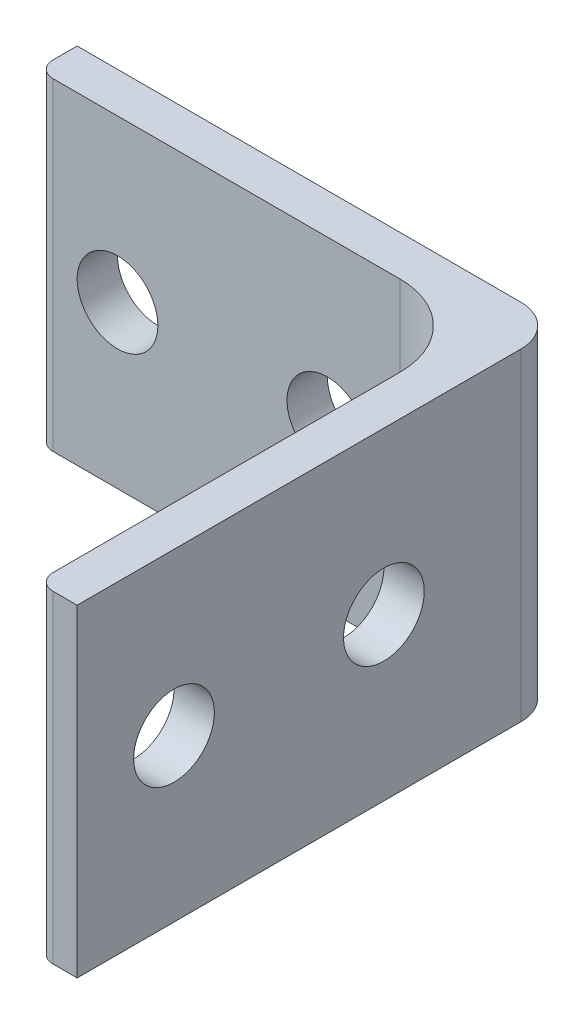
SolidWorks part; units mm, degrees
ref_plane "Front Plane" through (0, 0, 0) normal (0, 0, 1) x (1, 0, 0)
ref_plane "Top Plane" through (0, 0, 0) normal (0, 1, 0) x (1, 0, 0)
ref_plane "Right Plane" through (0, 0, 0) normal (1, 0, 0) x (0, 0, -1)
sketch "Sketch1" plane through (0, 0, 0) normal (0, 1, 0) x (1, 0, 0)
  line L0 (0, 0) -> (34.925, 0)
  line L1 (38.1, -3.175) -> (38.1, -38.1)
  line L2 (38.1, -38.1) -> (36.195, -38.1)
  line L3 (34.925, -36.83) -> (34.925, -9.525)
  line L4 (28.575, -3.175) -> (1.27, -3.175)
  line L5 (0, -1.905) -> (0, 0)
  arc A0 (34.925, -9.525) -> (28.575, -3.175) centre (28.575, -9.525) ccw
  arc A1 (34.925, 0) -> (38.1, -3.175) centre (34.925, -3.175) cw
  arc A2 (36.195, -38.1) -> (34.925, -36.83) centre (36.195, -36.83) cw
  arc A3 (1.27, -3.175) -> (0, -1.905) centre (1.27, -1.905) cw
  point P11 (38.1, 0)
  point P14 (34.925, -38.1)
  point P17 (0, -3.175)
  dimension "D5" = 6.35
  dimension "D6" = 3.175
  dimension "D7" = 1.27
  dimension "D1" = 3.175
  dimension "D2" = 3.175
  dimension "D3" = 38.1
  dimension "D4" = 38.1
extrude "Boss-Extrude1" add sketch "Sketch1" against normal blind 25.4
sketch "Sketch2" plane through (34.925, 0, 0) normal (-1, 0, 0) x (0, 0, 1)
  line L0 (36.83, -25.4) -> (36.83, 0) construction
  line L1 (9.525, 0) -> (36.83, 0) construction
  circle A0 centre (30.48, -12.7) radius 3.175
  circle A1 centre (13.97, -12.7) radius 3.175
  point P8 (20.6672, -13.169)
  dimension "D1" = 6.35
  dimension "D2" = 6.35
  dimension "D3" = 16.51
  dimension "D4" = 12.7
extrude "Cut-Extrude1" cut sketch "Sketch2" against normal blind 25.4
sketch "Sketch3" plane through (0, 0, 3.175) normal (0, 0, 1) x (1, 0, 0)
  line L0 (0, -25.4) -> (0, 0) construction
  line L1 (1.27, 0) -> (28.575, 0) construction
  circle A0 centre (6.35, -12.7) radius 3.175
  circle A1 centre (22.86, -12.7) radius 3.175
  dimension "D1" = 16.51
  dimension "D3" = 6.35
  dimension "D2" = 6.35
  dimension "D4" = 12.7
extrude "Cut-Extrude2" cut sketch "Sketch3" against normal blind 25.4
